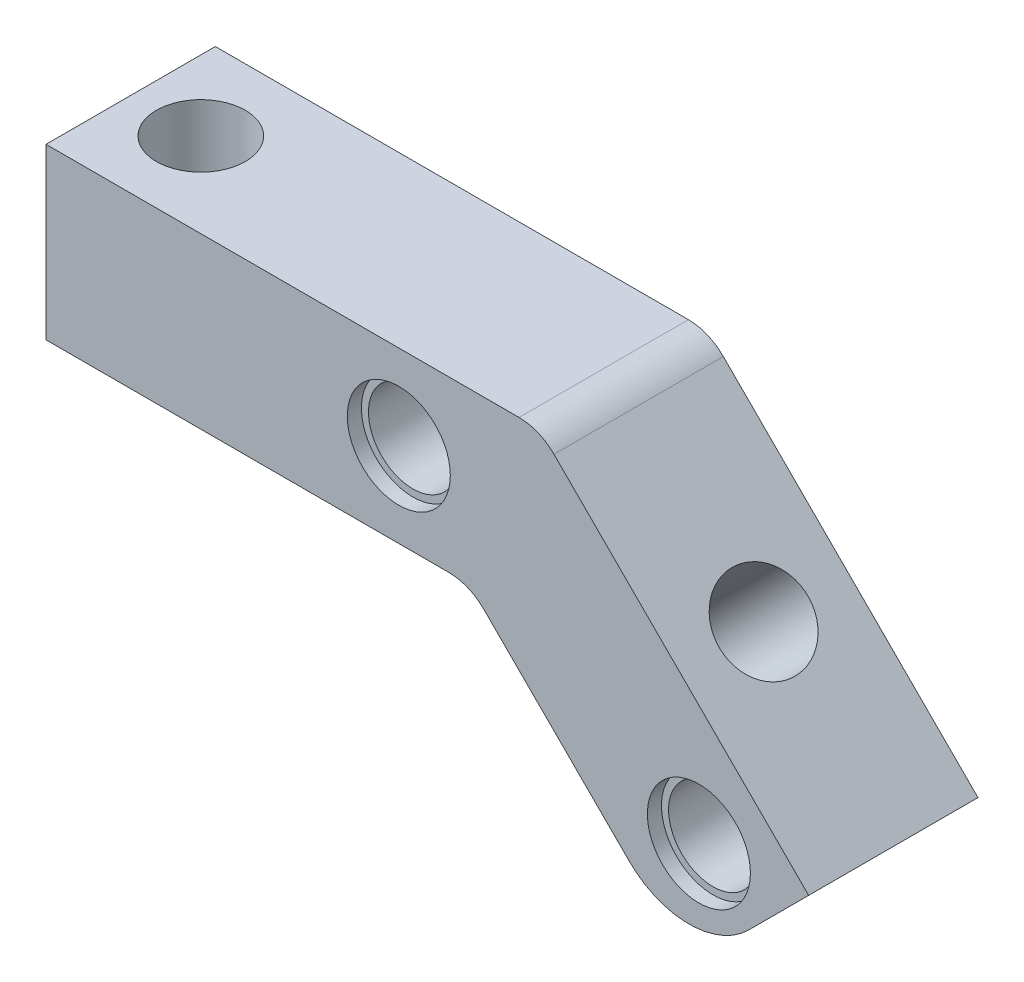
SolidWorks part; units mm, degrees
ref_plane "Front" through (0, 0, 0) normal (0, 0, 1) x (1, 0, 0)
ref_plane "Top" through (0, 0, 0) normal (0, 1, 0) x (1, 0, 0)
ref_plane "Right" through (0, 0, 0) normal (1, 0, 0) x (0, 0, -1)
sketch "Esquisse1" plane through (0, 0, 0) normal (0, 0, 1) x (1, 0, 0)
  line L0 (0, 0) -> (30, 0)
  line L1 (30, 0) -> (45.5563, -15.5563)
  line L2 (45.5563, -15.5563) -> (54.0416, -7.0711)
  line L3 (54.0416, -7.0711) -> (34.9706, 12)
  line L4 (34.9706, 12) -> (0, 12)
  line L5 (0, 12) -> (0, 0)
  dimension "D1" = 12
  dimension "D2" = 12
  dimension "D3" = 135
  dimension "D4" = 30
  dimension "D5" = 22
extrude "Boss.-Extru.1" add sketch "Esquisse1" along normal blind 12
sketch "Esquisse2" plane through (0, 0, 12) normal (0, 0, 1) x (1, 0, 0)
  line L0 (0, 6) -> (25, 6) construction
  line L1 (0, 12) -> (0, 0) construction
  line L2 (49.799, -11.3137) -> (46.2635, -7.7782) construction
  line L3 (45.5563, -15.5563) -> (54.0416, -7.0711) construction
  circle A0 centre (25, 6) radius 3.15
  circle A1 centre (46.2635, -7.7782) radius 3.15
  dimension "D1" = 6.3
  dimension "D2" = 25
  dimension "D3" = 5
extrude "Enlèv. mat.-Extru.1" cut sketch "Esquisse2" against normal through all both and the other way through all
sketch "Esquisse3" plane through (23.4853, 23.4853, 0) normal (0.7071, 0.7071, 0) x (0, 0, -1)
  line L0 (-6, -43.2132) -> (-6, -30.2132) construction
  line L1 (-12, -43.2132) -> (0, -43.2132) construction
  circle A0 centre (-6, -30.2132) radius 3.15
  dimension "D2" = 6.3
  dimension "D1" = 13
extrude "Enlèv. mat.-Extru.2" cut sketch "Esquisse3" against normal blind 12
sketch "Esquisse4" plane through (0, 12, 0) normal (0, 1, 0) x (1, 0, 0)
  line L0 (34.9706, -6) -> (4.9706, -6) construction
  line L1 (34.9706, -12) -> (34.9706, 0) construction
  circle A0 centre (4.9706, -6) radius 3.15
  dimension "D1" = 6.3
  dimension "D2" = 30
extrude "Enlèv. mat.-Extru.3" cut sketch "Esquisse4" against normal through all both and the other way through all
sketch "Esquisse5" plane through (0, 0, 12) normal (0, 0, 1) x (1, 0, 0)
  circle A0 centre (25, 6) radius 3.65
  circle A1 centre (46.2635, -7.7782) radius 3.65
  dimension "D1" = 7.3
extrude "Enlèv. mat.-Extru.4" cut sketch "Esquisse5" against normal blind 1
sketch "Esquisse6" plane through (0, 0, 0) normal (0, 0, -1) x (-1, 0, 0)
  circle A0 centre (-25, 6) radius 3.65
  circle A1 centre (-46.2635, -7.7782) radius 3.65
  dimension "D1" = 7.3
extrude "Enlèv. mat.-Extru.5" cut sketch "Esquisse6" against normal blind 1
sketch "Esquisse7" plane through (15, 15, 0) normal (-0.7071, -0.7071, 0) x (0, 0, 1)
  circle A0 centre (6, -30.2132) radius 3.65
  dimension "D1" = 7.3
extrude "Enlèv. mat.-Extru.6" cut sketch "Esquisse7" against normal blind 1
sketch "Esquisse8" plane through (0, 0, 0) normal (0, -1, 0) x (1, 0, 0)
  circle A0 centre (4.9706, 6) radius 3.65
  dimension "D1" = 7.3
extrude "Enlèv. mat.-Extru.7" cut sketch "Esquisse8" against normal blind 1
fillet "Congé1" radius 3.5 2 edges at (34.9706, 12, 6) (30, 0, 6)
fillet "Congé2" radius 6 1 edges at (45.5563, -15.5563, 6)
